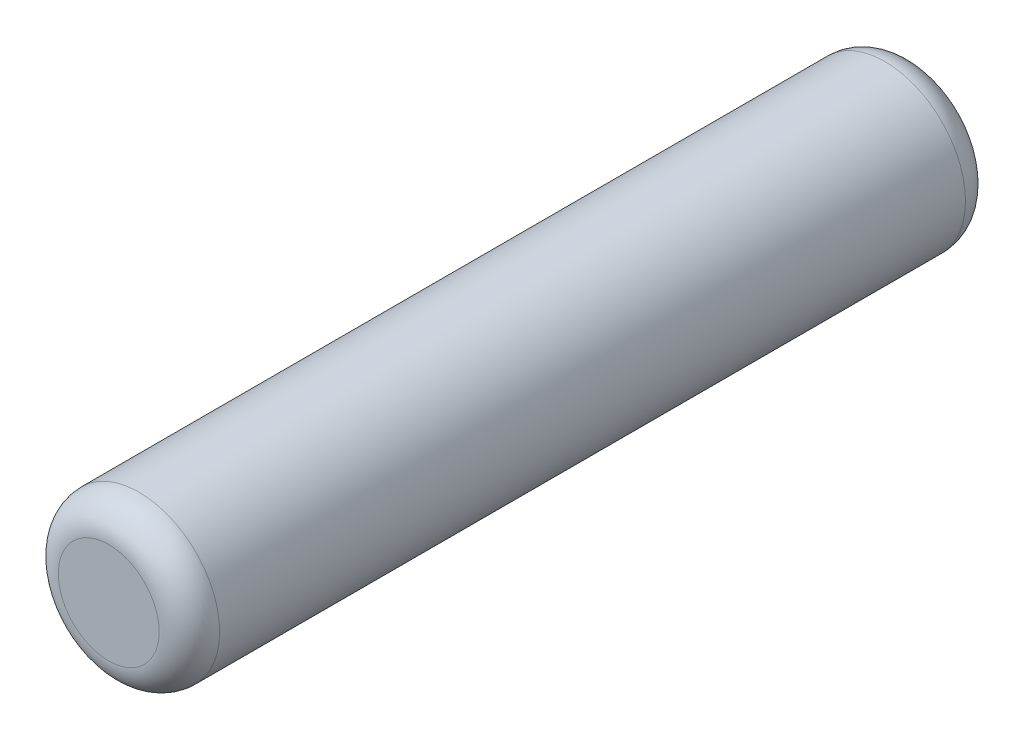
SolidWorks part; units mm, degrees
material "Stub"
ref_plane "Face" through (0, 0, 0) normal (0, 0, 1) x (1, 0, 0)
ref_plane "Dessus" through (0, 0, 0) normal (0, 1, 0) x (1, 0, 0)
ref_plane "Droite" through (0, 0, 0) normal (1, 0, 0) x (0, 0, -1)
sketch "Esquisse1" plane through (0, 0, 0) normal (0, 0, 1) x (1, 0, 0)
  circle A0 centre (0, 0) radius 4
  dimension "D1" = 8
extrude "Boss.-Extru.1" add sketch "Esquisse1" along normal mid plane 40
fillet "Congé1" radius 1.5 2 edges at (4, 0, -20) (4, 0, 20)
